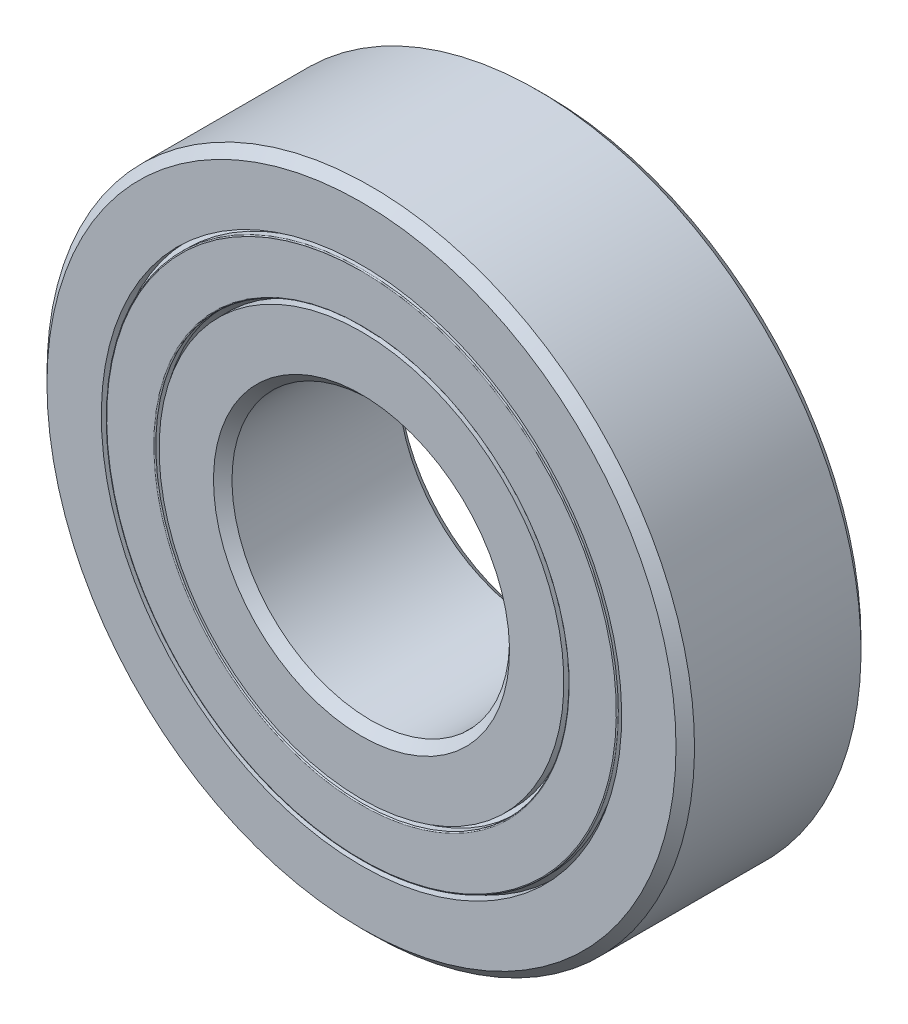
SolidWorks part; units mm, degrees
material "Plain Carbon Steel"
ref_plane "Front Plane" through (0, 0, 0) normal (0, 0, 1) x (1, 0, 0)
ref_plane "Top Plane" through (0, 0, 0) normal (0, 1, 0) x (1, 0, 0)
ref_plane "Right Plane" through (0, 0, 0) normal (1, 0, 0) x (0, 0, -1)
sketch "Sketch1" plane through (0, 0, 0) normal (0, 0, 1) x (1, 0, 0)
  line L0 (-14, 0) -> (14, 0) construction
  line L1 (-6, 0) -> (6, 0) construction
  circle A0 centre (0, 0) radius 6 construction
  circle A1 centre (0, 0) radius 14 construction
  point P3 (0, 0)
  point P6 (0, 0)
  point P7 (0, -6)
  point P11 (0, -14)
  point P12 (0, 6)
  point P13 (0, 14)
  dimension "OD" = 28
  dimension "ID" = 12
sketch "Sketch2" plane through (0, 0, 0) normal (1, 0, 0) x (0, 0, -1)
  line L0 (-4, 14) -> (4, 14) construction
  line L1 (0, 14) -> (0, -14) construction
  line L2 (3.6, 14) -> (-3.6, 14)
  line L3 (-3.6, 14) -> (-4, 13.6)
  line L4 (-4, 13.6) -> (-4, 11.25)
  line L5 (-4, 11.25) -> (-1.7778, 11.25)
  line L6 (4, 11.25) -> (1.7778, 11.25)
  line L7 (4, 13.6) -> (4, 11.25)
  line L8 (3.6, 14) -> (4, 13.6)
  line L9 (0, 14) -> (0, 10) construction
  line L10 (0, 10) -> (0, 6) construction
  line L11 (0, 14) -> (0, -14) construction
  line L12 (-4, 0) -> (4, 0) construction
  line L13 (4, 6) -> (-4, 6) construction
  line L14 (0, 12.1732) -> (0, 7.8268) construction
  line L15 (-4, -6) -> (4, -6) construction
  line L16 (-4, 6) -> (-4, -6) construction
  line L17 (4, 14) -> (4, -14) construction
  line L18 (-4, 11.25) -> (-4, 11.125) construction
  line L19 (-4, 11.125) -> (-4, 11) construction
  line L20 (-4, 11) -> (-4, 10.875) construction
  line L21 (-4, 10.875) -> (-4, 10.75) construction
  line L22 (-4, 10.75) -> (-4, 10.625) construction
  line L24 (-2.8889, 11.25) -> (-2.8889, 10) construction
  arc A0 (-1.7778, 11.25) -> (1.7778, 11.25) centre (0, 10) cw
  circle A1 centre (0, 10) radius 2.1732 construction
  point P14 (0, 6)
  point P17 (0, 0)
  point P21 (0, 14)
  point P29 (0, 6)
  point P30 (0, -6)
  point P46 (-2.8889, 10.625)
  dimension "Width" = 8
  dimension "D1" = 45
  dimension "D2" = 0.4
  dimension "D3" = 3.5556
  dimension "D4" = 1.25
  dimension "For Shaft Diameter" = 12
  dimension "For Housing ID" = 28
sketch "Sketch3" plane through (0, 0, 0) normal (1, 0, 0) x (0, 0, -1)
  line L0 (3.6, 14) -> (4, 13.6) construction
  line L1 (4, 13.6) -> (4, 11.25) construction
  line L2 (4, 11.25) -> (1.7778, 11.25) construction
  line L3 (-4, 11.25) -> (-1.7778, 11.25) construction
  line L4 (-4, 13.6) -> (-4, 11.25) construction
  line L5 (-3.6, 14) -> (-4, 13.6) construction
  line L6 (3.6, 14) -> (-3.6, 14) construction
  line L7 (3.6, 14) -> (4, 13.6)
  line L8 (4, 13.6) -> (4, 11.25)
  line L9 (4, 11.25) -> (1.7778, 11.25)
  line L10 (-4, 11.25) -> (-1.7778, 11.25)
  line L11 (-4, 13.6) -> (-4, 11.25)
  line L12 (-3.6, 14) -> (-4, 13.6)
  line L13 (3.6, 14) -> (-3.6, 14)
  arc A0 (1.7778, 11.25) -> (-1.7778, 11.25) centre (0, 10) ccw construction
  arc A1 (1.7778, 11.25) -> (-1.7778, 11.25) centre (0, 10) ccw
revolve "Revolve1" add sketch "Sketch3" angle 360 about L12
sketch "Sketch4" plane through (0, 0, 0) normal (1, 0, 0) x (0, 0, -1)
  line L0 (0, 14) -> (0, -14) construction
  line L1 (0, 14) -> (0, -14) construction
  line L2 (-3.6, 6) -> (-4, 6.4)
  line L3 (-4, 6.4) -> (-4, 8.75)
  line L5 (-4, 8.75) -> (-1.7778, 8.75)
  line L6 (-3.6, 6) -> (3.6, 6)
  line L8 (3.6, 6) -> (4, 6.4)
  line L10 (4, 6.4) -> (4, 8.75)
  line L11 (4, 8.75) -> (1.7778, 8.75)
  line L12 (-4, 13.6) -> (-4, 11.25) construction
  line L13 (3.6, 14) -> (4, 13.6) construction
  line L15 (4, -13.6) -> (4, 13.6) construction
  line L16 (3.6, 14) -> (3.6, -14) construction
  arc A1 (1.7778, 8.75) -> (-1.7778, 8.75) centre (0, 10) cw
  circle A2 centre (0, 10) radius 2.1732 construction
  point P1 (0, 6)
revolve "Revolve2" add sketch "Sketch4" angle 360 about L12
sketch "Sketch5" plane through (0, 0, 0) normal (1, 0, 0) x (0, 0, -1)
  line L0 (-2.1732, 10) -> (2.1732, 10)
  arc A2 (-2.1732, 10) -> (2.1732, 10) centre (0, 10) cw
  arc A3 (1.7778, 11.25) -> (-1.7778, 11.25) centre (0, 10) ccw construction
revolve "Revolve3" add sketch "Sketch5" angle 360 about L0
sketch "Sketch6" plane through (0, 0, 0) normal (1, 0, 0) x (0, 0, -1)
  line L0 (-4, 11.25) -> (-4, 10.625) construction
  line L1 (-4, 13.6) -> (-4, -13.6) construction
  line L2 (-4, 10.625) -> (-4, 10) construction
  line L3 (-4, 10) -> (-4, 9.375) construction
  line L4 (-4, 9.375) -> (-4, 8.75) construction
  line L5 (-4, 10.625) -> (-3.6802, 10.625) construction
  line L7 (-2.0814, 10.625) -> (-2.0814, 9.375) construction
  line L8 (-3.6802, 10.625) -> (-3.3605, 10.625) construction
  line L10 (0, 14) -> (0, -14) construction
  line L11 (0, 14) -> (0, -14) construction
  line L12 (-3.3605, 10.625) -> (-3.0407, 10.625) construction
  line L13 (-3.0407, 10.625) -> (-2.721, 10.625) construction
  line L14 (-2.721, 10.625) -> (-2.4012, 10.625) construction
  line L15 (-2.4012, 10.625) -> (-2.0814, 10.625) construction
  line L16 (-2.0814, 10.625) -> (-2.4012, 10.625)
  line L17 (-2.4012, 9.375) -> (-2.721, 9.375) construction
  line L18 (-2.4012, 9.375) -> (-2.0814, 9.375)
  line L19 (-2.721, 9.375) -> (-2.721, 10.625) construction
  line L20 (-2.5611, 10.625) -> (-2.5611, 9.375) construction
  circle A0 centre (0, 10) radius 2.1732 construction
  circle A1 centre (0, 10) radius 2.1732 construction
  arc A2 (-2.4012, 10.625) -> (-2.4012, 9.375) centre (-1.2595, 10) ccw
  arc A3 (-2.0814, 10.625) -> (-2.0814, 9.375) centre (0, 10) ccw
  point P28 (-2.5611, 10)
revolve "Revolve4" add sketch "Sketch6" angle 360 about L11
pattern_circular "CirPattern1" count 8 over 360 about axis through (0, 0, 0) along (0, 0, 1) of bodies 134 104
sketch "Sketch7" plane through (0, 0, 0) normal (0, 0, 1) x (1, 0, 0)
  line L0 (0, 8.75) -> (0, 9.1667) construction
  line L1 (0, 7.8268) -> (0, 12.1732) construction
  line L2 (0, 9.1667) -> (0, 9.5833) construction
  line L3 (0, 9.5833) -> (0, 10) construction
  line L4 (0, 10) -> (0, 10.4167) construction
  line L5 (0, 10.4167) -> (0, 10.8333) construction
  line L6 (0, 10.8333) -> (0, 11.25) construction
  line L7 (0, 13.6) -> (0, 11.25) construction
  line L8 (0, 14) -> (0, -14) construction
  circle A0 centre (0, 0) radius 8.75 construction
  circle A1 centre (0, 0) radius 10
  circle A2 centre (0, 0) radius 10.625
  point P19 (0, 10.625)
extrude "Boss-Extrude1" add sketch "Sketch7" along normal mid plane 1.3333 separate body
sketch "Sketch8" plane through (0, 0, 0) normal (1, 0, 0) x (0, 0, -1)
  line L0 (-4, 11.125) -> (-4, 11) construction
  line L1 (-4, 11.0625) -> (-3.7037, 11.0625)
  line L2 (-4, 11.0625) -> (-4, 8.9375)
  line L3 (-4, 8.9375) -> (-3.7037, 8.9375)
  line L4 (-3.5556, 11.0625) -> (-3.5556, 8.9375)
  line L5 (0, 14) -> (0, 10) construction
  line L10 (-3.7037, 11.0625) -> (-3.5556, 11.25)
  line L11 (-4, 11.25) -> (-1.7778, 11.25) construction
  line L12 (-3.5556, 11.25) -> (-3.5556, 11.0625)
  line L13 (-3.7037, 8.9375) -> (-3.5556, 8.75)
  line L14 (-3.5556, 8.75) -> (-3.5556, 8.9375)
  line L15 (-4, 11.25) -> (-3.8519, 11.25) construction
  line L16 (4, 11.0625) -> (4, 8.9375)
  line L17 (4, 8.9375) -> (3.7037, 8.9375)
  line L18 (3.7037, 8.9375) -> (3.5556, 8.75)
  line L19 (3.5556, 8.75) -> (3.5556, 8.9375)
  line L20 (3.5556, 11.0625) -> (3.5556, 8.9375)
  line L21 (3.5556, 11.25) -> (3.5556, 11.0625)
  line L22 (3.7037, 11.0625) -> (3.5556, 11.25)
  line L23 (4, 11.0625) -> (3.7037, 11.0625)
  line L24 (-3.8519, 11.25) -> (-3.7037, 11.25) construction
  line L25 (-3.7037, 11.25) -> (-3.5556, 11.25) construction
  line L27 (-4, 8.75) -> (-1.7778, 8.75) construction
  point P23 (-4, 11.0625)
  dimension "D1" = 0.4444
revolve "Revolve5" add sketch "Sketch8" angle 360 about L12
fillet "Fillet1" radius 0.0444 2 edges at (0, -11.0625, 4) (0, -8.9375, 4)
fillet "Fillet2" radius 0.0444 2 edges at (0, -8.9375, -4) (0, -11.0625, -4)
equation "\"D2@Sketch2\" = \"Width@Sketch2\" * .05"
equation "\"D3@Sketch2\" = \"Width@Sketch2\" / 2.25"
equation "\"D4@Sketch2\"=( \"OD@Sketch1\" - \"Width@Sketch2\" )  *.5*.125"
equation "\"D1@Boss-Extrude1\" = \"Width@Sketch2\" / 6"
equation "\"D1@Sketch8\"=(\"Width@Sketch2\"-\"D3@Sketch2\")*.5*.2"
equation "\"D1@Fillet1\"=\"d1@sketch8\"*.1"
equation "\"D1@Fillet2\"=\"d1@fillet1\""
